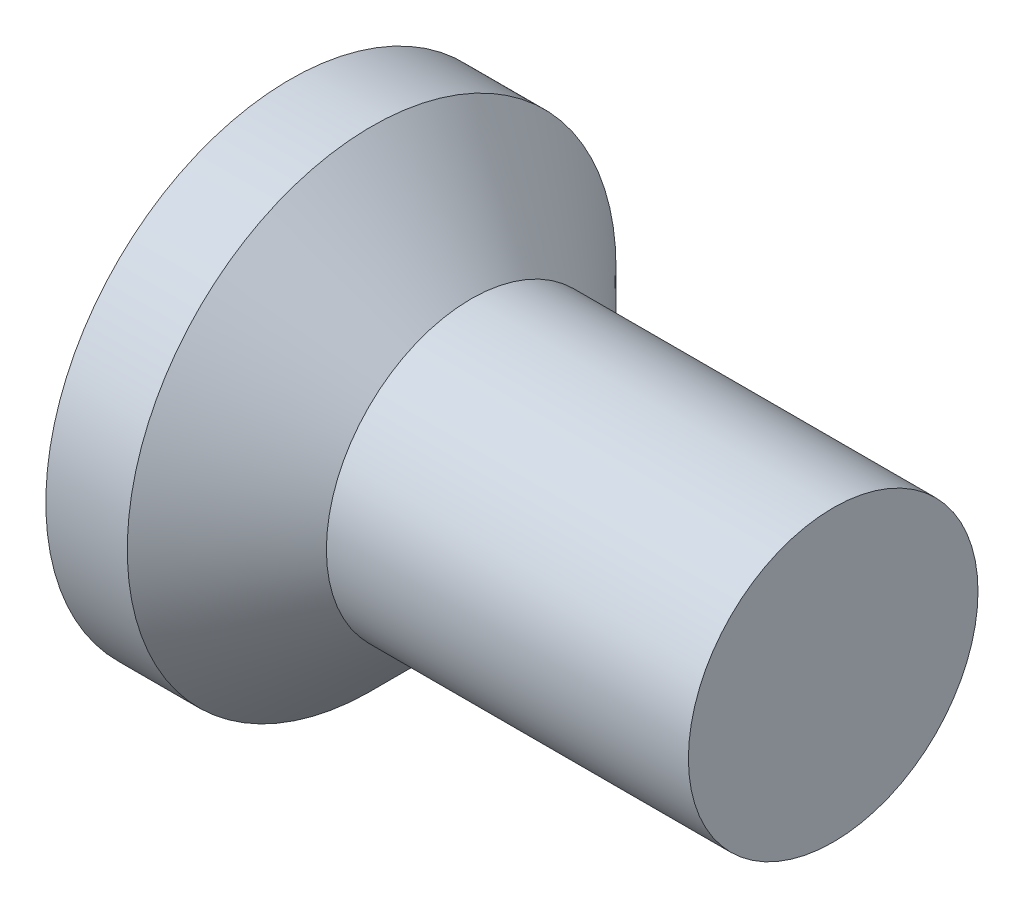
SolidWorks part; units mm, degrees
ref_plane "Front" through (0, 0, 0) normal (0, 0, 1) x (1, 0, 0)
ref_plane "Top" through (0, 0, 0) normal (0, 1, 0) x (1, 0, 0)
ref_plane "Right" through (0, 0, 0) normal (1, 0, 0) x (0, 0, -1)
sketch "Sketch1" plane through (0, 0, 0) normal (0, 0, 1) x (1, 0, 0)
  line L0 (3, 0.8) -> (1.7, 0.8)
  line L1 (1.7, 0.8) -> (1, 0.8)
  line L2 (1, 0.8) -> (0.45, 1.35)
  line L3 (0.45, 1.35) -> (0, 1.35)
  line L4 (3, 0.8) -> (3, 0)
  line L5 (4.5158, 0) -> (-89.8219, 0) construction
  line L6 (3, 0) -> (0, 0)
  line L7 (0, 1.35) -> (0, 0)
  dimension "D1" = 45
  dimension "dk" = 2.7
  dimension "l" = 3
  dimension "k" = 1
  dimension "a" = 0.7
  dimension "d" = 1.6
revolve "Base" add sketch "Sketch1" angle 360 about L5
cosmetic thread "ThreadCosmetic1" [suppressed] parameters "bb"=2
sketch "Sketch6" plane through (0, 0, 0) normal (1, 0, 0) x (0, 0, -1)
  line L0 (-1.9271, 0) -> (2.0512, 0) construction
  line L1 (0, 1.8651) -> (0, -2.0207) construction
  line L2 (0.16, 0.16) -> (0.16, 0.8)
  line L3 (0.16, 0.8) -> (-0.16, 0.8)
  line L4 (-0.16, 0.16) -> (-0.16, 0.8)
  line L5 (0.16, 0.16) -> (0.8, 0.16)
  line L6 (0.8, 0.16) -> (0.8, -0.16)
  line L7 (-0.8, 0.16) -> (-0.8, -0.16)
  line L8 (-0.16, 0.16) -> (-0.8, 0.16)
  line L9 (-0.16, -0.16) -> (-0.8, -0.16)
  line L10 (0.16, -0.16) -> (0.8, -0.16)
  line L11 (-0.16, -0.16) -> (-0.16, -0.8)
  line L12 (0.16, -0.8) -> (-0.16, -0.8)
  line L13 (0.16, -0.16) -> (0.16, -0.8)
  point P16 (-0.8, 0)
  point P17 (0.8, 0)
extrude "CrossRecess" cut sketch "Sketch6" along normal blind 0.5
draft "Draft9" type of draft neutral plane draft angle 30 faces to draft 4 face at (0.25, 0.8, 0) face at (0.25, 0, 0.8) face at (0.25, -0.8, 0) face at (0.25, 0, -0.8) neutral plane through (0, 1.35, 0) neutral plane normal (-1, 0, 0) parameters "D1"=30
fillet "Fillet5" radius 0.3 4 edges at (0.25, -0.16, -0.16) (0.25, 0.16, -0.16) (0.25, 0.16, 0.16) (0.25, -0.16, 0.16)
sketch "Sketch7" plane through (0, 0, 0) normal (1, 0, 0) x (0, 0, -1)
  line L0 (-2.0126, 0) -> (1.9757, 0) construction
  line L1 (0, 1.9314) -> (0, -2.0126) construction
  line L2 (0, 0) -> (1.5555, 1.5555) construction
  line L3 (0, 0.2391) -> (0.5657, 0.5657)
  line L4 (-1.5402, 1.5402) -> (0, 0) construction
  line L5 (0.2391, 0) -> (0.5657, 0.5657)
  line L6 (0, -0.2391) -> (0.5657, -0.5657)
  line L7 (0.2391, 0) -> (0.5657, -0.5657)
  line L8 (-0.2391, 0) -> (-0.5657, -0.5657)
  line L9 (0, -0.2391) -> (-0.5657, -0.5657)
  line L10 (-0.2391, 0) -> (-0.5657, 0.5657)
  line L11 (0, 0.2391) -> (-0.5657, 0.5657)
  dimension "D3" = 15
  dimension "m" = 1.6
extrude "Cut-Extrude3" [suppressed] cut sketch "Sketch7" along normal blind 10 draft 20
sketch "Sketch8" plane through (0, 0, 0) normal (0, 0, 1) x (1, 0, 0)
  line L0 (-22, 0.9895) -> (-22.9, 0.8)
  line L1 (-22.9, 0.8) -> (1, 0.8)
  line L3 (3, -0.8) -> (3, 0.8) construction
  line L6 (1, 0.8) -> (1, 5.8)
  line L7 (1, 5.8) -> (-22, 5.8)
  line L8 (-22, 5.8) -> (-22, 0.9895)
  line L9 (62.4753, 0.1895) -> (52.9594, 0.1895) construction
  dimension "D1" = 5
  dimension "x" = 0.9
  dimension "d" = 1.6
  dimension "THD_MINOR" = 1.221
  dimension "b" = 25
sketch "Sketch9" plane through (0, 0, 0) normal (0, 0, 1) x (1, 0, 0)
  line L0 (3, 0.6359) -> (3.0948, 0.8)
  line L1 (3.0948, 0.8) -> (3.0948, 0.9895)
  line L2 (3.0948, 0.9895) -> (2.9053, 0.9895)
  line L3 (2.9053, 0.9895) -> (2.9053, 0.8)
  line L4 (2.9053, 0.8) -> (3, 0.6359)
  line L5 (0, 0) -> (73.843, 0) construction
  line L6 (3, -0.8) -> (3, 0.8) construction
  dimension "D1" = 1.6
  dimension "D2" = 0.1895
revolve "Cut-Revolve10" [suppressed] cut sketch "Sketch9" angle 360 about L5
pattern_linear "LPattern10" [suppressed] count 9 spacing 0.2274 along (1, 0, 0)
equation "\"D1@Sketch6\" = \"m@Sketch6\" / 5"
equation "\"D1@CrossRecess\" = \"k@Sketch1\" / 2"
equation "\"D1@Sketch9\" = \"d@Sketch1\""
equation "\"D2@Sketch9\" =  ( \"d@Sketch1\" - \"THD_MINOR@ThreadCosmetic1\" )  / 2"
equation "\"D3@LPattern10\" = \"D2@Sketch9\" * 1.2"
equation "\"D1@LPattern10\" = \"bb@ThreadCosmetic1\" / \"D3@LPattern10\" "
